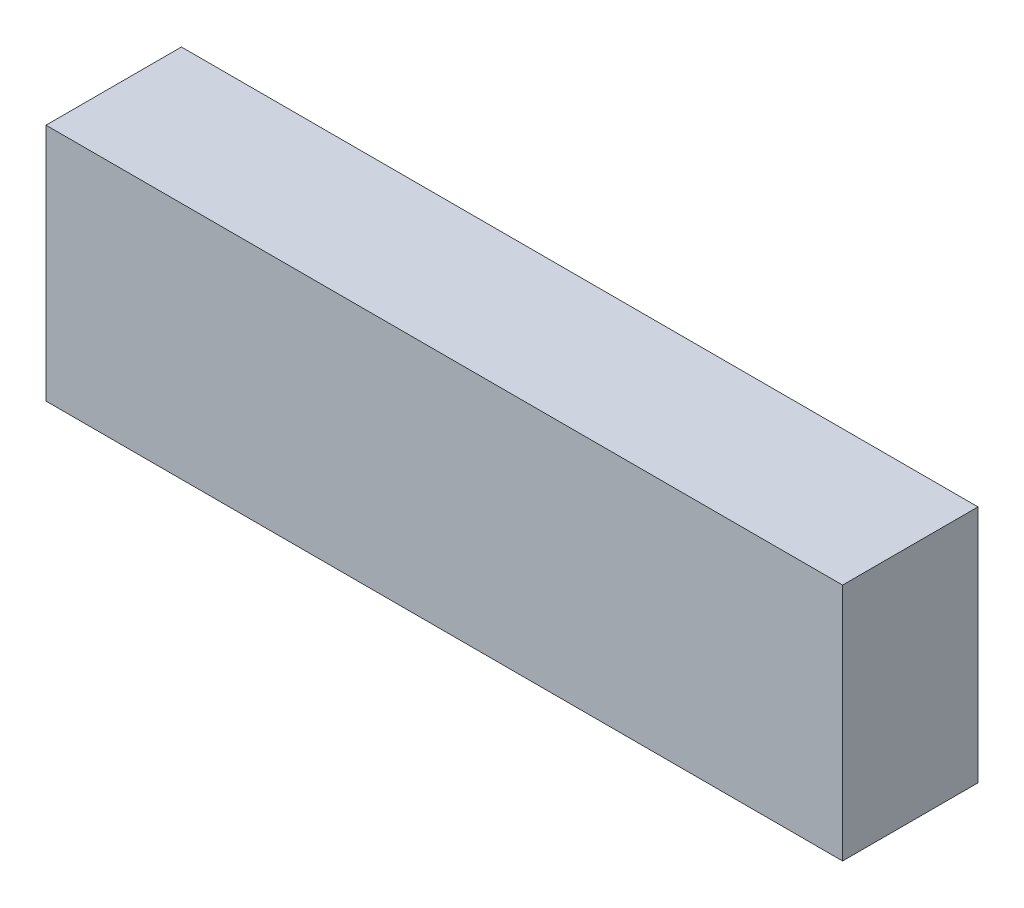
SolidWorks part; units mm, degrees
material "鎳"
ref_plane "前基準面" through (0, 0, 0) normal (0, 0, 1) x (1, 0, 0)
ref_plane "上基準面" through (0, 0, 0) normal (0, 1, 0) x (1, 0, 0)
ref_plane "右基準面" through (0, 0, 0) normal (1, 0, 0) x (0, 0, -1)
sketch "草圖1" plane through (0, 0, 0) normal (0, 0, 1) x (1, 0, 0)
  line L1 (-50, 15) -> (50, 15)
  line L2 (-50, 15) -> (-50, -15)
  line L3 (-50, -15) -> (50, -15)
  line L4 (50, 15) -> (50, -15)
  line L5 (-50, 15) -> (50, -15) construction
  line L6 (-50, -15) -> (50, 15) construction
  point P0 (0, 0)
  dimension "D1" = 100
  dimension "D2" = 30
extrude "填料-伸長1" add sketch "草圖1" along normal blind 17
sketch3d "URDF Reference"
  line L0 (0, 0, 0) -> (10, 0, 0) construction
  line L1 (0, 0, 0) -> (0, 0, -10) construction
  point P0 (0, 0, 0)
  point P1 (0, 0, 0)
